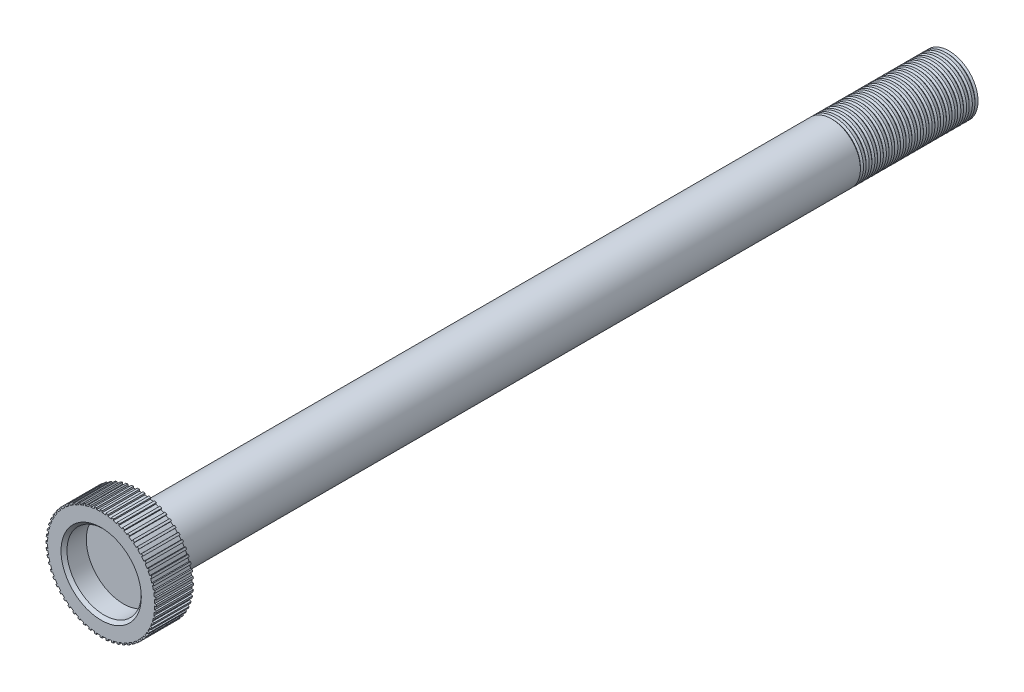
SolidWorks part; units mm, degrees
ref_plane "Front Plane" through (0, 0, 0) normal (0, 0, 1) x (1, 0, 0)
ref_plane "Top Plane" through (0, 0, 0) normal (0, 1, 0) x (1, 0, 0)
ref_plane "Right Plane" through (0, 0, 0) normal (1, 0, 0) x (0, 0, -1)
sketch "Sketch1" plane through (0, 0, 0) normal (0, 0, 1) x (1, 0, 0)
  circle A0 centre (0, 0) radius 9.144
  dimension "D1" = 18.288
extrude "Extrude1" add sketch "Sketch1" along normal blind 6.35
sketch "Sketch2" plane through (0, 0, 6.35) normal (0, 0, 1) x (1, 0, 0)
  circle A0 centre (0, 0) radius 6.35
  dimension "D1" = 12.7
extrude "Cut-Extrude1" cut sketch "Sketch2" against normal blind 3.81
chamfer "Chamfer1" distance 0.508 angle 45 1 edges at (6.35, 0, 6.35)
sketch "Sketch3" plane through (0, 0, 0) normal (0, 0, -1) x (-1, 0, 0)
  circle A0 centre (0, 0) radius 4.953
  dimension "D1" = 9.906
extrude "Extrude2" add sketch "Sketch3" along normal blind 138.43
sketch "Sketch4" plane through (0, 0, 0) normal (0, 0, 1) x (1, 0, 0)
  line L1 (-0.1751, 9.4203) -> (0.1751, 9.4203)
  line L2 (-0.1751, 9.4203) -> (-0.1751, 8.9755)
  line L3 (-0.1751, 8.9755) -> (0.1751, 8.9755)
  line L4 (0.1751, 9.4203) -> (0.1751, 8.9755)
extrude "Extrude3" add sketch "Sketch4" along normal up to surface (6.35 mm away) up to face at (6.858, 0, 6.35)
pattern_circular "CirPattern1" count 60 over 360 about axis through (0, 0, 0) along (0, 0, 1) of "Extrude3"
sketch "Sketch5" plane through (0, 0, 0) normal (0, 1, 0) x (1, 0, 0)
  line L0 (-4.953, 138.43) -> (-4.6877, 138.1647)
  line L1 (4.953, 138.43) -> (-4.953, 138.43) construction
  line L2 (-4.6877, 138.1647) -> (-4.953, 137.8993)
  line L3 (-4.953, 138.43) -> (-4.953, 0) construction
  line L4 (-4.953, 137.8993) -> (-5.2183, 138.1647)
  line L5 (-5.2183, 138.1647) -> (-4.953, 138.43)
revolve "Cut-Revolve1" cut sketch "Sketch5" angle 360 about axis through (0, 0, -138.43) along (0, 0, 1)
pattern_linear "LPattern1" count 21 spacing 0.978 along (0, 0, 1) of "Cut-Revolve1"
